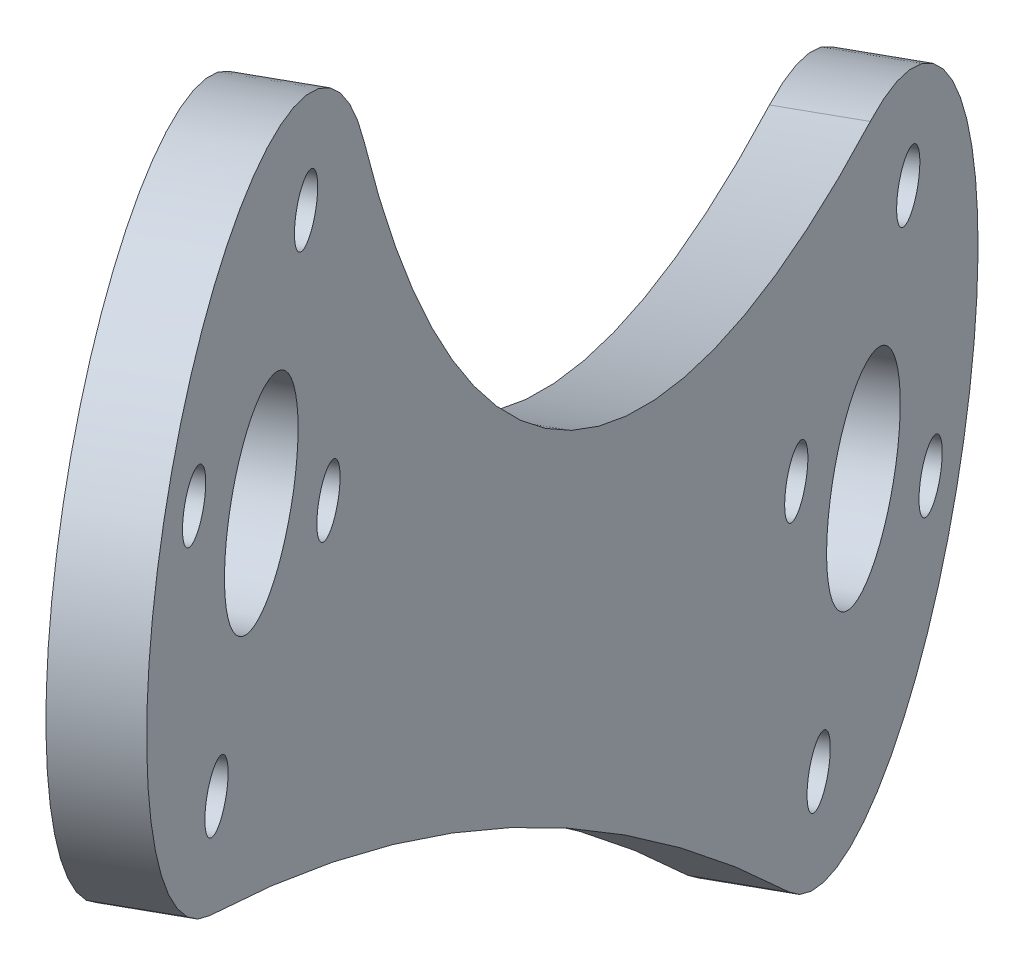
SolidWorks part; units mm, degrees
material "1345 Alloy"
ref_plane "Front Plane" through (0, 0, 0) normal (0, 0, 1) x (1, 0, 0)
ref_plane "Top Plane" through (0, 0, 0) normal (0, 1, 0) x (1, 0, 0)
ref_plane "Right Plane" through (0, 0, 0) normal (1, 0, 0) x (0, 0, -1)
ref_plane "Plane1" through (22.0669, 0, -12.3377) normal (-0.8728, 0, 0.488) x (0, -1, 0)
sketch "Sketch1" plane through (22.0669, 0, -12.3377) normal (-0.8728, 0, 0.488) x (0, -1, 0)
  arc A0 (-72.9479, 167.8978) -> (-37.4244, 114.6213) centre (-100.8116, 110.8377) cw
  arc A1 (-37.4244, 114.6213) -> (-16.2203, 123.1919) centre (-25.3808, 115.3402) ccw
  arc A2 (-16.2203, 123.1919) -> (-56.8836, 184.1769) centre (215.2044, 321.5493) cw
  arc A3 (-56.8836, 184.1769) -> (-72.9479, 167.8978) centre (-67.6538, 178.7393) ccw
  circle A4 centre (-32.453, 110.6247) radius 1.2192
  circle A5 centre (-20.6653, 108.2681) radius 1.2192
  circle A6 centre (-18.3087, 120.0558) radius 1.2192
  circle A7 centre (-30.0964, 122.4124) radius 1.2192
  circle A8 centre (-62.9382, 171.6671) radius 1.2192
  circle A9 centre (-60.5816, 183.4548) radius 1.2192
  circle A10 centre (-72.3693, 185.8114) radius 1.2192
  circle A11 centre (-74.7259, 174.0237) radius 1.2192
  circle A12 centre (-67.6538, 178.7393) radius 3.8735
  circle A13 centre (-25.3808, 115.3402) radius 3.8735
extrude "Boss-Extrude1" add sketch "Sketch1" against normal blind 3
